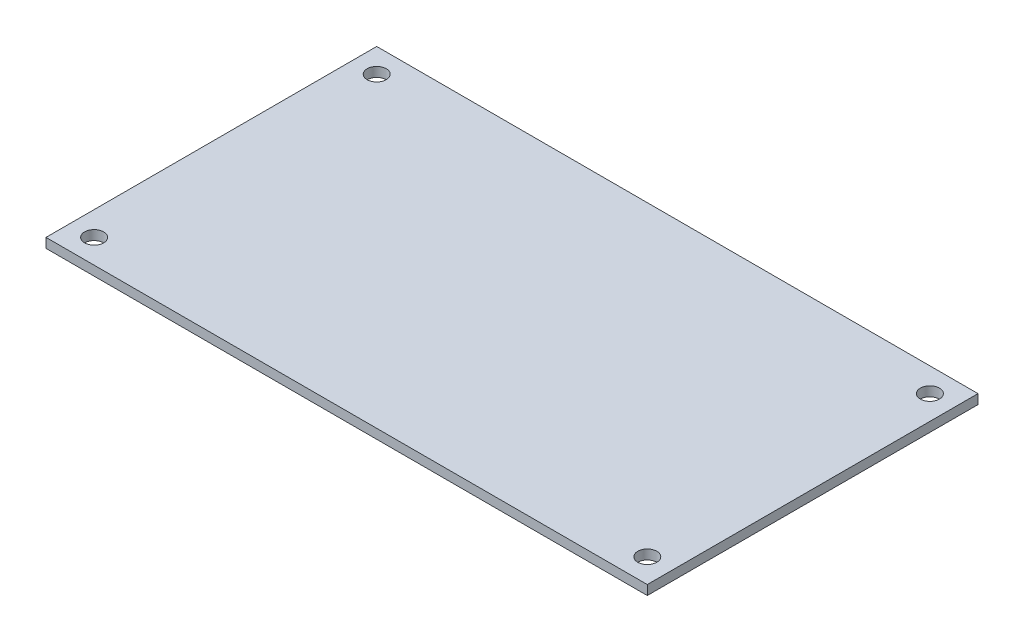
SolidWorks part; units mm, degrees
ref_plane "Front Plane" through (0, 0, 0) normal (0, 0, 1) x (1, 0, 0)
ref_plane "Top Plane" through (0, 0, 0) normal (0, 1, 0) x (1, 0, 0)
ref_plane "Right Plane" through (0, 0, 0) normal (1, 0, 0) x (0, 0, -1)
sketch "Sketch1" plane through (0, 0, 0) normal (0, 1, 0) x (1, 0, 0)
  line L1 (0, 0) -> (200, 0)
  line L2 (0, 0) -> (0, 110)
  line L3 (0, 110) -> (200, 110)
  line L4 (200, 0) -> (200, 110)
  dimension "D1" = 110
  dimension "D2" = 200
extrude "Boss-Extrude1" add sketch "Sketch1" along normal blind 3.175
sketch "Sketch2" plane through (0, 3.175, 0) normal (0, 1, 0) x (1, 0, 0)
  line L0 (200, 110) -> (0, 110) construction
  line L1 (0, 110) -> (0, 0) construction
  line L2 (100, 0) -> (100, 110) construction
  line L3 (0, 0) -> (200, 0) construction
  line L4 (0, 55) -> (200, 55) construction
  line L5 (200, 0) -> (200, 110) construction
  circle A0 centre (8, 102) radius 3.175
  circle A1 centre (192, 102) radius 3.175
  circle A2 centre (192, 8) radius 3.175
  circle A3 centre (8, 8) radius 3.175
  dimension "D1" = 6.35
  dimension "D2" = 8
  dimension "D3" = 8
extrude "Cut-Extrude1" cut sketch "Sketch2" against normal up to next
equation "\"base_plate_width\"=110"
equation "\"D1@Sketch1\"=\"base_plate_width\""
